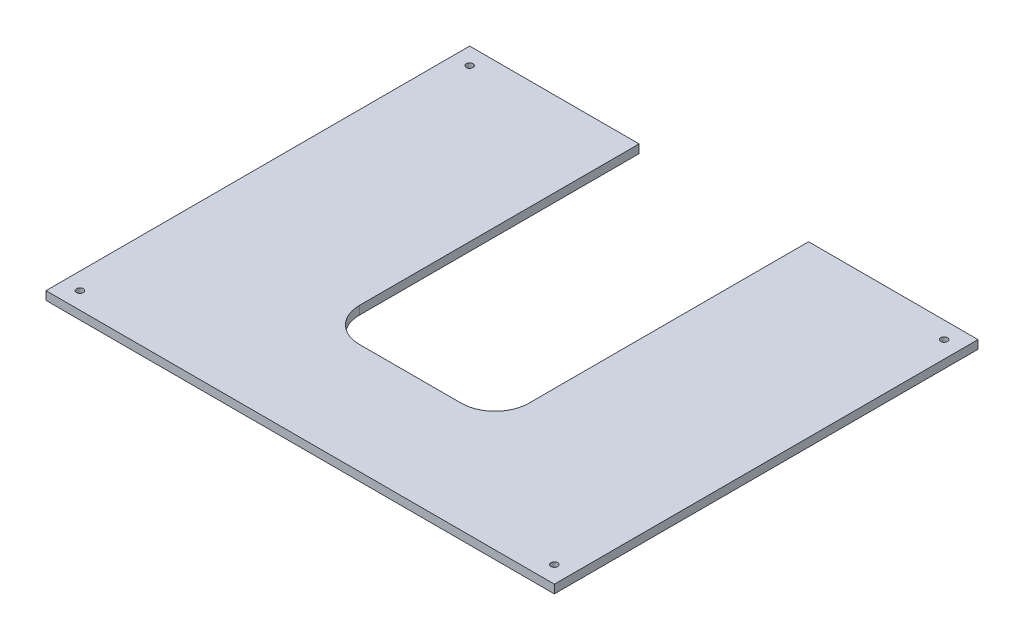
SolidWorks part; units mm, degrees
ref_plane "前视基准面" through (0, 0, 0) normal (0, 0, 1) x (1, 0, 0)
ref_plane "上视基准面" through (0, 0, 0) normal (0, 1, 0) x (1, 0, 0)
ref_plane "右视基准面" through (0, 0, 0) normal (1, 0, 0) x (0, 0, -1)
sketch "Sketch1" plane through (0, 0, 0) normal (0, 1, 0) x (1, 0, 0)
  line L0 (-140, -125) -> (-140, 125) construction
  line L1 (-150, -125) -> (150, -125)
  line L2 (-150, -125) -> (-150, 125)
  line L3 (-150, 125) -> (150, 125)
  line L4 (150, -125) -> (150, 125)
  line L5 (-150, -125) -> (150, 125) construction
  line L6 (-150, 125) -> (150, -125) construction
  line L7 (0, 0) -> (0, 125) construction
  line L8 (0, 0) -> (-150, 0) construction
  circle A0 centre (-140, -115) radius 2
  circle A1 centre (-140, 115) radius 2
  circle A2 centre (140, -115) radius 2
  circle A3 centre (140, 115) radius 2
  point P0 (0, 0)
  dimension "D4" = 4
  dimension "D5" = 10
  dimension "D1" = 300
  dimension "D2" = 250
  dimension "D3" = 10
extrude "Boss-Extrude1" add sketch "Sketch1" along normal blind 5
sketch "Sketch2" plane through (0, 5, 0) normal (0, 1, 0) x (1, 0, 0)
  line L0 (150, 125) -> (-150, 125) construction
  line L1 (-50, 125) -> (50, 125)
  line L2 (-50, 125) -> (-50, -60)
  line L3 (-50, -60) -> (50, -60)
  line L4 (50, 125) -> (50, -60)
  line L5 (0, -60) -> (0, 125) construction
  dimension "D1" = 100
  dimension "D2" = 185
extrude "Cut-Extrude1" cut sketch "Sketch2" against normal through all
fillet "Fillet1" radius 20 2 edges at (50, 2.5, 60) (-50, 2.5, 60)
